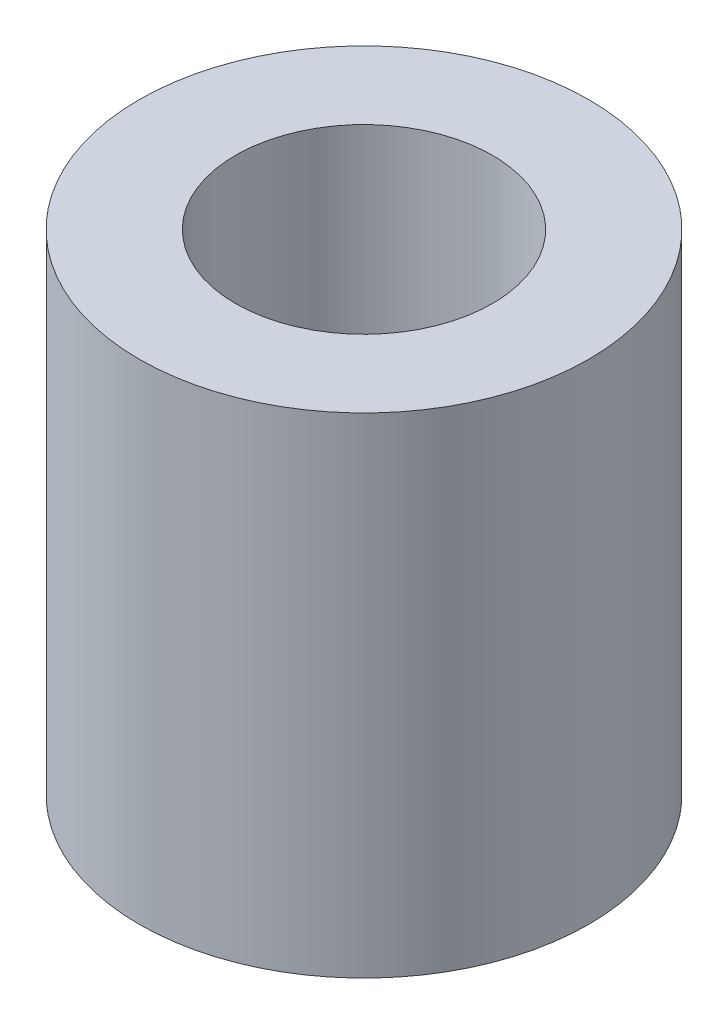
SolidWorks part; units mm, degrees
material "6061-T6 (SS)"
ref_plane "X-Y Datum" through (0, 0, 0) normal (0, 0, 1) x (1, 0, 0)
ref_plane "X-Z Datum" through (0, 0, 0) normal (0, 1, 0) x (1, 0, 0)
ref_plane "Y-Z Datum" through (0, 0, 0) normal (1, 0, 0) x (0, 0, -1)
sketch "Sketch1" plane through (0, 0, 0) normal (0, 1, 0) x (1, 0, 0)
  circle A0 centre (0, 0) radius 2
  circle A1 centre (0, 0) radius 3.5
  dimension "D1" = 4
  dimension "D2" = 7
  dimension "D3" = 1.5
extrude "Boss-Extrude1" add sketch "Sketch1" against normal blind 7.62
